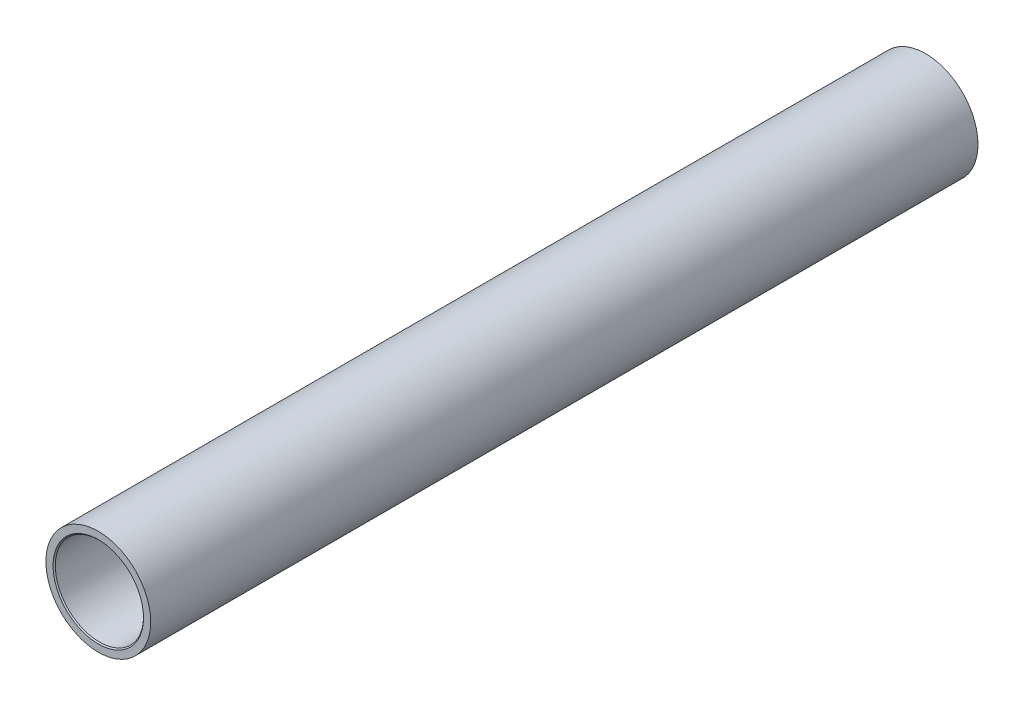
SolidWorks part; units mm, degrees
other "DetailItem1"
other "DetailItem2"
other "Weld Folder"
other "Weld Bead1"
other "Weld Bead2"
material "Alloy Steel"
ref_plane "Ön Düzlem" through (0, 0, 0) normal (0, 0, 1) x (1, 0, 0)
ref_plane "Üst Düzlem" through (0, 0, 0) normal (0, 1, 0) x (1, 0, 0)
ref_plane "Sağ Düzlem" through (0, 0, 0) normal (1, 0, 0) x (0, 0, -1)
sketch "Sketch1" plane through (0, 0, 0) normal (0, 0, 1) x (1, 0, 0)
  circle A0 centre (0, 0) radius 47.5
  circle A1 centre (0, 0) radius 40
  dimension "D1" = 95
  dimension "D2" = 80
extrude "Boss-Extrude1" add sketch "Sketch1" along normal mid plane 750
cosmetic thread "Cosmetic Thread1" parameters "D1"=50, "D2"=80.5
ref_plane "Plane1" through (0, -47.5, 0) normal (0, -1, 0) x (-1, 0, 0)
sketch "Sketch2" plane through (0, -47.5, 0) normal (0, -1, 0) x (-1, 0, 0)
  line L0 (0, 479.1914) -> (0, -452.2591) construction
  line L1 (0, 375) -> (0, 342)
  line L2 (47.5, 375) -> (-47.5, 375) construction
  circle A0 centre (0, 342) radius 5
  dimension "D1" = 33
extrude "Cut-Extrude1" cut sketch "Sketch2" against normal blind 20 contours L1 L0 A0 | L0 L1 A0
sketch "Sketch3" plane through (0, -47.5, 0) normal (0, -1, 0) x (-1, 0, 0)
  circle A0 centre (0, 342) radius 5
  circle A1 centre (0, 342) radius 10
extrude "Boss-Extrude2" add sketch "Sketch3" along normal blind 5
sketch "Sketch4" plane through (0, -47.5, 0) normal (0, -1, 0) x (-1, 0, 0)
  circle A0 centre (0, 342) radius 5
  circle A1 centre (0, 342) radius 10
extrude "Boss-Extrude3" add sketch "Sketch4" against normal up to surface separate body up to face at (1.1189, -47.4868, -337.1268)
chamfer "Chamfer1" distance 1 angle 45 2 edges at (40, 0, 375) (40, 0, -375)
